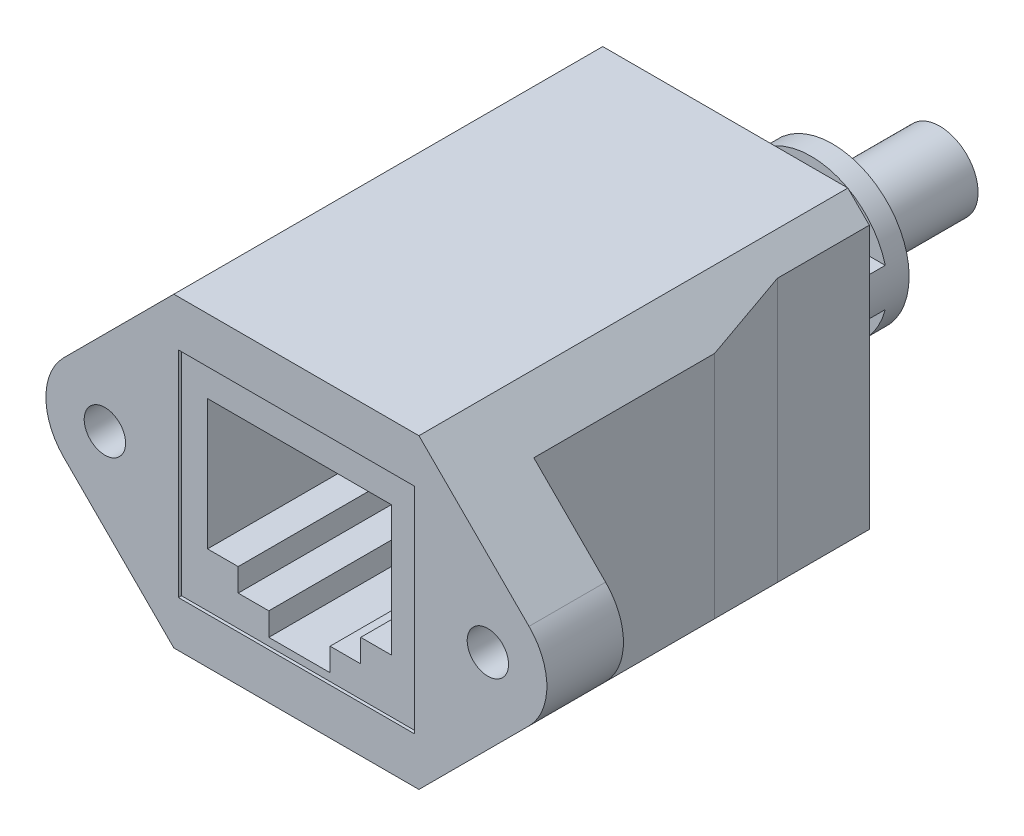
SolidWorks part; units mm, degrees
ref_plane "Front Plane" through (0, 0, 0) normal (0, 0, 1) x (1, 0, 0)
ref_plane "Top Plane" through (0, 0, 0) normal (0, 1, 0) x (1, 0, 0)
ref_plane "Right Plane" through (0, 0, 0) normal (1, 0, 0) x (0, 0, -1)
sketch "Sketch1" plane through (0, 0, 0) normal (0, 0, 1) x (1, 0, 0)
  line L0 (8, 10) -> (18, 0)
  line L1 (-8, -10) -> (8, -10)
  line L2 (-8, -10) -> (-8, 10) construction
  line L3 (-8, 10) -> (8, 10)
  line L4 (8, -10) -> (8, 10) construction
  line L5 (-8, -10) -> (8, 10) construction
  line L6 (-8, 10) -> (8, -10) construction
  line L7 (18, 0) -> (8, -10)
  line L8 (-8, 10) -> (-18, 0)
  line L9 (-18, 0) -> (-8, -10)
  line L10 (-18, 0) -> (-8, 0) construction
  line L11 (8, 0) -> (18, 0) construction
  point P0 (0, 0)
  dimension "D1" = 20
  dimension "D3" = 16
extrude "Boss-Extrude1" add sketch "Sketch1" against normal blind 28 contours L3 L0 L7 L1 L9 L8
sketch "Sketch2" plane through (0, 0, 0) normal (0, 1, 0) x (1, 0, 0)
  line L0 (-18, 5) -> (-10.5, 5)
  line L1 (-18, 28) -> (-18, 0) construction
  line L2 (-10.5, 5) -> (-10.5, 16.8)
  line L3 (-10.5, 16.8) -> (-9.4, 22)
  line L4 (-9.4, 22) -> (-9.4, 28)
  line L5 (-9.4, 28) -> (-18, 28)
  line L6 (-18, 28) -> (-18, 5)
  line L7 (-8, 0) -> (-18, 0) construction
  dimension "D1" = 22
  dimension "D2" = 10.5
  dimension "D3" = 5
  dimension "D4" = 9.4
  dimension "D5" = 16.8
extrude "Cut-Extrude1" cut sketch "Sketch2" against normal through all and the other way through all
mirror "Mirror1" about plane through (0, 0, 0) normal (1, 0, 0) of "Cut-Extrude1"
sketch "Sketch3" plane through (0, 0, 0) normal (0, 0, 1) x (1, 0, 0)
  line L0 (-12.5, 0) -> (12.5, 0) construction
  circle A0 centre (-12.5, 0) radius 1.35
  circle A1 centre (12.5, 0) radius 1.35
  point P4 (0, 0)
  dimension "D2" = 2.7
  dimension "D1" = 25
extrude "Cut-Extrude2" cut sketch "Sketch3" against normal up to next
fillet "Fillet1" radius 3.98 2 edges at (-18, 0, -2.5) (18, 0, -2.5)
sketch "Sketch4" plane through (0, 0, -28) normal (0, 0, -1) x (-1, 0, 0)
  circle A0 centre (0, 0) radius 5
  dimension "D1" = 10
extrude "Boss-Extrude2" add sketch "Sketch4" along normal blind 7
sketch "Sketch6" plane through (0, 0, 0) normal (1, 0, 0) x (0, 0, -1)
  line L0 (29.4, 5) -> (28, 5) construction
  line L1 (29.4, 5) -> (30.8, 5)
  line L2 (29.4, 5) -> (29.4, 1.25)
  line L3 (29.4, 1.25) -> (30.8, 1.25)
  line L4 (30.8, 5) -> (30.8, 1.25)
  line L5 (32.2, 5) -> (33.6, 5)
  line L6 (32.2, 5) -> (32.2, 1.25)
  line L7 (32.2, 1.25) -> (33.6, 1.25)
  line L8 (33.6, 5) -> (33.6, 1.25)
  line L9 (30.8, 5) -> (32.2, 5) construction
  line L10 (33.6, 5) -> (35, 5) construction
  dimension "D1" = 1.25
extrude "Cut-Extrude3" cut sketch "Sketch6" against normal through all and the other way through all
mirror "Mirror2" about plane through (0, 0, 0) normal (0, 1, 0) of "Cut-Extrude3"
sketch "Sketch5" plane through (0, 0, -35) normal (0, 0, -1) x (-1, 0, 0)
  circle A0 centre (0, 0) radius 2.5
  dimension "D1" = 5
extrude "Boss-Extrude3" add sketch "Sketch5" along normal blind 7 and the other way blind 7
sketch "Sketch7" plane through (0, 0, 0) normal (0, 0, 1) x (1, 0, 0)
  line L1 (-7.7, -7) -> (7.7, -7)
  line L2 (-7.7, -7) -> (-7.7, 7)
  line L3 (-7.7, 7) -> (7.7, 7)
  line L4 (7.7, -7) -> (7.7, 7)
  line L5 (-7.7, -7) -> (7.7, 7) construction
  line L6 (-7.7, 7) -> (7.7, -7) construction
  point P0 (0, 0)
  dimension "D1" = 15.4
  dimension "D2" = 14
extrude "Cut-Extrude4" cut sketch "Sketch7" against normal blind 0.2
sketch "Sketch8" plane through (0, 0, -0.2) normal (0, 0, 1) x (1, 0, 0)
  line L0 (-6, 5) -> (6, 5)
  line L1 (6, 5) -> (6, -3.5)
  line L2 (6, -3.5) -> (4, -3.5)
  line L3 (4, -3.5) -> (4, -5)
  line L4 (4, -5) -> (2, -5)
  line L5 (2, -5) -> (2, -6.5)
  line L6 (2, -6.5) -> (-2, -6.5)
  line L7 (-2, -6.5) -> (-2, -5)
  line L8 (-2, -5) -> (-4, -5)
  line L9 (-4, -5) -> (-4, -3.5)
  line L10 (-4, -3.5) -> (-6, -3.5)
  line L11 (-6, -3.5) -> (-6, 5)
  line L12 (0, 0) -> (0, 5) construction
  line L13 (7.7, 7) -> (-7.7, 7) construction
  dimension "D1" = 12
  dimension "D2" = 8
  dimension "D3" = 4
  dimension "D4" = 1.5
  dimension "D5" = 1.5
  dimension "D6" = 2
  dimension "D7" = 11.5
extrude "Cut-Extrude5" cut sketch "Sketch8" against normal blind 12
